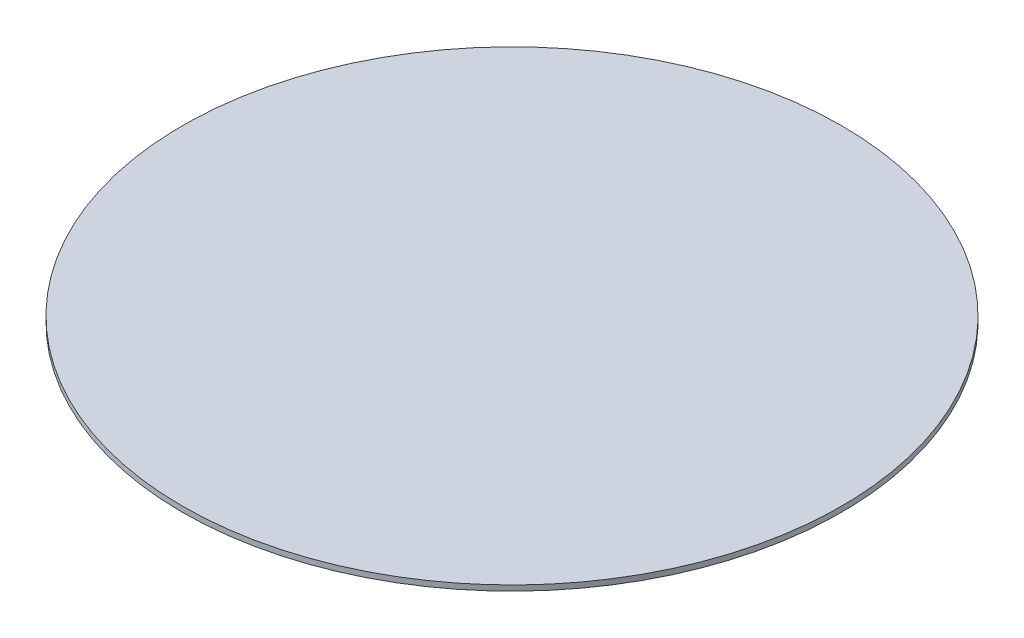
SolidWorks part; units mm, degrees
material "Glass"
ref_plane "Front Plane" through (0, 0, 0) normal (0, 0, 1) x (1, 0, 0)
ref_plane "Top Plane" through (0, 0, 0) normal (0, 1, 0) x (1, 0, 0)
ref_plane "Right Plane" through (0, 0, 0) normal (1, 0, 0) x (0, 0, -1)
sketch "Sketch1" plane through (0, 0, 0) normal (0, 1, 0) x (1, 0, 0)
  circle A0 centre (0, 0) radius 127
  dimension "D1" = 254
extrude "Boss-Extrude1" add sketch "Sketch1" along normal blind 2.07
